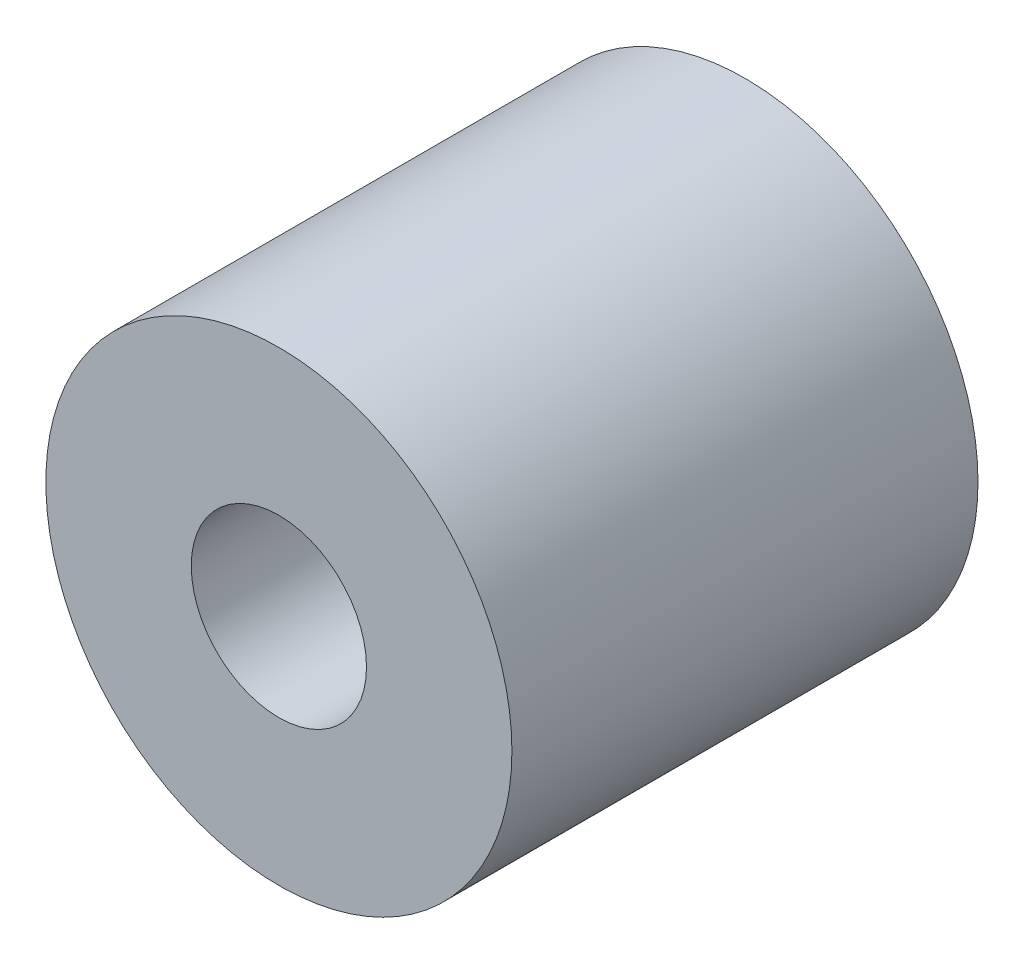
SolidWorks part; units mm, degrees
material "Tin Bearing Bronze"
ref_plane "Front Plane" through (0, 0, 0) normal (0, 0, 1) x (1, 0, 0)
ref_plane "Top Plane" through (0, 0, 0) normal (0, 1, 0) x (1, 0, 0)
ref_plane "Right Plane" through (0, 0, 0) normal (1, 0, 0) x (0, 0, -1)
sketch "Sketch1" plane through (0, 0, 0) normal (0, 0, 1) x (1, 0, 0)
  circle A0 centre (0, 0) radius 3.175
  circle A1 centre (0, 0) radius 1.1938
  dimension "D1" = 6.35
  dimension "ID" = 2.3876
extrude "Extrude1" add sketch "Sketch1" along normal mid plane 6.35
sketch "Sketch2" plane through (0, 0, 0) normal (1, 0, 0) x (0, 0, -1)
  line L0 (-3.175, -1.1938) -> (3.175, -1.1938) construction
  line L3 (3.175, 1.1938) -> (-3.175, 1.1938) construction
  line L5 (-3.175, -1.1938) -> (3.175, -1.1938)
  line L6 (3.175, 1.1938) -> (-3.175, 1.1938)
sketch "Sketch4" plane through (0, 0, 3.175) normal (0, 0, 1) x (1, 0, 0)
  line L0 (0, 0) -> (-0.8441, 0.8441)
  line L1 (0, -48.895) -> (0, 48.895) construction
  circle A0 centre (0, 0) radius 1.1938 construction
  dimension "D1" = 45
